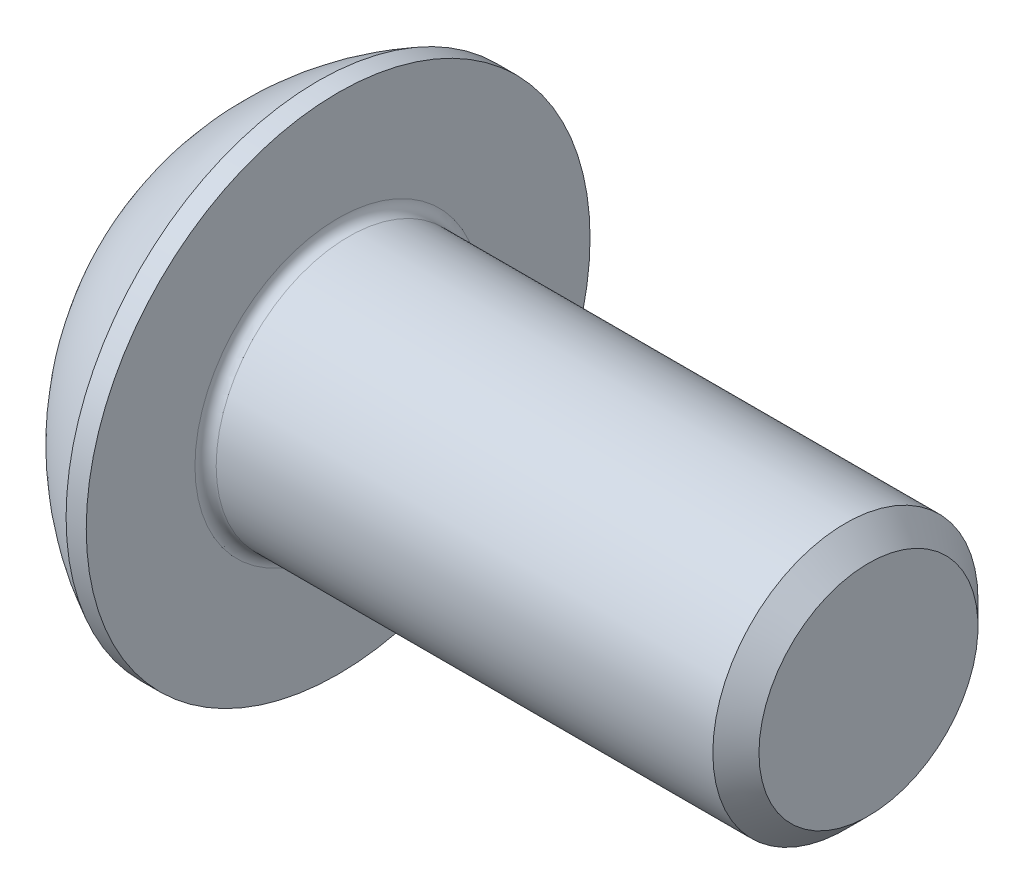
SolidWorks part; units mm, degrees
ref_plane "Plane1" through (0, 0, 0) normal (0, 0, 1) x (1, 0, 0)
ref_plane "Plane2" through (0, 0, 0) normal (0, 1, 0) x (1, 0, 0)
ref_plane "Plane3" through (0, 0, 0) normal (1, 0, 0) x (0, 0, -1)
sketch "BodySke" plane through (0, 0, 0) normal (0, 0, 1) x (1, 0, 0)
  line L0 (12.75, 0) -> (12.75, 2.065)
  line L1 (12.315, 2.5) -> (2.75, 2.5)
  line L2 (2.75, 2.5) -> (2.75, 4.75)
  line L3 (2.75, 4.75) -> (2.37, 4.75)
  line L4 (0, 0) -> (101.6, 0) construction
  line L5 (2.75, -4.75) -> (2.37, -4.75) construction
  line L6 (55.6768, -2.5) -> (2.75, -2.5) construction
  line L7 (12.75, 0) -> (0, 0)
  line L8 (0, 2.375) -> (0, -2.375) construction
  line L9 (0, 0) -> (0, 2.375)
  line L10 (12.75, 2.065) -> (12.315, 2.5)
  line L11 (12.75, -2.065) -> (12.315, -2.5) construction
  line L12 (3.45, 9.525) -> (3.45, -2.5) construction
  line L13 (3.75, 9.525) -> (3.75, -2.5) construction
  arc A1 (0, 2.375) -> (2.37, 4.75) centre (4.755, 0) cw
  dimension "Diameter" = 5
  dimension "Length" = 10
  dimension "Head_dia" = 9.5
  dimension "D1" = 4.75
  dimension "Head_ht" = 2.75
  dimension "Head_side_ht" = 0.38
  dimension "Minor_dia" = 4.13
  dimension "Body_ch_ang" = 45
  dimension "Advance" = 0.7
  dimension "Thread_nom" = 9
revolve "BaseBody" add sketch "BodySke" angle 360 about L4
cosmetic thread "Representação de rosca1" parameters "D1"=29.8, "D2"=3.22
fillet "Fillet1" radius 0.2 1 edges at (2.75, 0, 2.5)
sketch "Sketch2" plane through (0, 0, 0) normal (0, 0, 1) x (1, 0, 0)
  line L0 (0, 1.25) -> (1.3, 1.25)
  line L1 (1.3, 1.25) -> (2.0217, 0)
  line L3 (2.0217, 0) -> (0, 0)
  line L4 (0, 0) -> (0, 1.25)
  line L5 (0, -1.25) -> (1.3, -1.25) construction
  line L6 (0, 0) -> (47.625, 0) construction
  dimension "D2" = 60
  dimension "PreBroach_depth" = 1.3
  dimension "PreBroach_dia" = 2.5
revolve "PreBroach" cut sketch "Sketch2" angle 360 about L6
sketch "Sketch3" plane through (0, 0, 0) normal (1, 0, 0) x (0, 0, -1)
  line L0 (-1.5, -0.866) -> (-1.5, 0.866)
  line L1 (-1.5, 0.866) -> (0, 1.7321)
  line L2 (0, 1.7321) -> (1.5, 0.866)
  line L3 (1.5, 0.866) -> (1.5, -0.866)
  line L4 (1.5, -0.866) -> (0, -1.7321)
  line L5 (0, -1.7321) -> (-1.5, -0.866)
  dimension "Hex_size" = 3
  dimension "D3" = 3
  dimension "D1" = 1.5
  dimension "D2" = 1.5
extrude "Hex" cut sketch "Sketch3" along normal blind 1.5
equation "\"D1@BodySke\" = \"Head_dia@BodySke\" * .5"
equation "\"D1@Sketch3\" = \"Hex_size@Sketch3\" / 2"
equation "\"D2@Sketch3\" = \"D1@Sketch3\""
equation "\"D3@Sketch3\" = \"Hex_size@Sketch3\""
